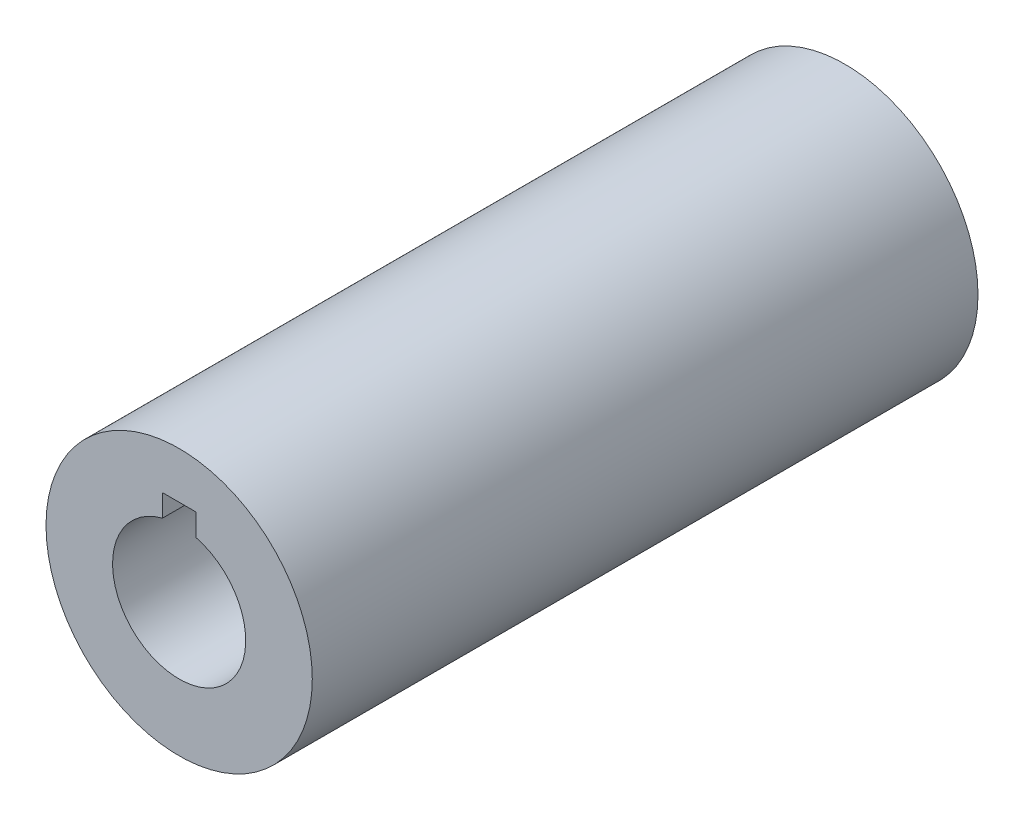
SolidWorks part; units mm, degrees
ref_plane "Front Plane" through (0, 0, 0) normal (0, 0, 1) x (1, 0, 0)
ref_plane "Top Plane" through (0, 0, 0) normal (0, 1, 0) x (1, 0, 0)
ref_plane "Right Plane" through (0, 0, 0) normal (1, 0, 0) x (0, 0, -1)
sketch "Sketch1" plane through (0, 0, 0) normal (0, 0, 1) x (1, 0, 0)
  line L1 (2.5, 9.6825) -> (2.5, 13)
  line L2 (-2.5, 9.6825) -> (-2.5, 13)
  line L3 (-2.5, 13) -> (2.5, 13)
  arc A0 (-2.5, 9.6825) -> (2.5, 9.6825) centre (0, 0) ccw
  circle A1 centre (0, 0) radius 20
  point P6 (0, 0)
extrude "Boss-Extrude1" add sketch "Sketch1" along normal mid plane 100
